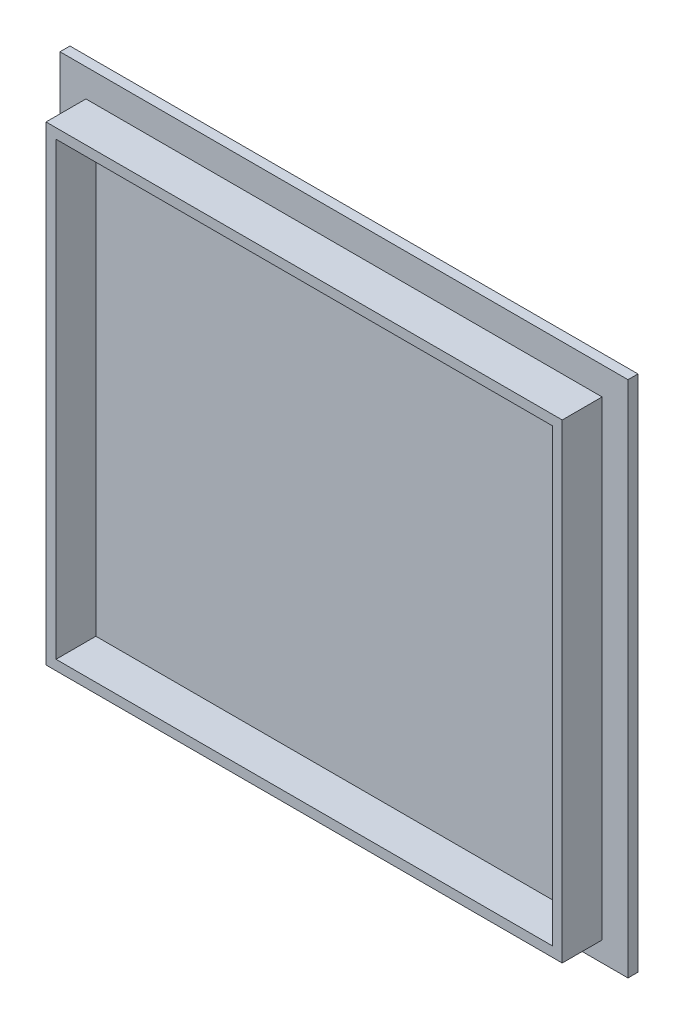
SolidWorks part; units mm, degrees
ref_plane "Front Plane" through (0, 0, 0) normal (0, 0, 1) x (1, 0, 0)
ref_plane "Top Plane" through (0, 0, 0) normal (0, 1, 0) x (1, 0, 0)
ref_plane "Right Plane" through (0, 0, 0) normal (1, 0, 0) x (0, 0, -1)
sketch "Sketch1" plane through (0, 0, 0) normal (0, 0, 1) x (1, 0, 0)
  line L1 (-121.8145, 173.0477) -> (163.1855, 173.0477)
  line L2 (-121.8145, 173.0477) -> (-121.8145, -86.9523)
  line L3 (-121.8145, -86.9523) -> (163.1855, -86.9523)
  line L4 (163.1855, 173.0477) -> (163.1855, -86.9523)
  dimension "D1" = 285
  dimension "D2" = 260
extrude "Boss-Extrude3" add sketch "Sketch1" along normal blind 5
sketch "Sketch3" plane through (0, 0, 5) normal (0, 0, 1) x (1, 0, 0)
  line L0 (163.1855, 173.0477) -> (-121.8145, 173.0477) construction
  line L1 (-108.8145, 159.0477) -> (150.1855, 159.0477)
  line L2 (-108.8145, 159.0477) -> (-108.8145, -76.9523)
  line L3 (-108.8145, -76.9523) -> (150.1855, -76.9523)
  line L4 (150.1855, 159.0477) -> (150.1855, -76.9523)
  line L5 (-121.8145, -86.9523) -> (163.1855, -86.9523) construction
  line L6 (-121.8145, 173.0477) -> (-121.8145, -86.9523) construction
  line L7 (163.1855, -86.9523) -> (163.1855, 173.0477) construction
  dimension "D1" = 14
  dimension "D2" = 10
  dimension "D3" = 13
  dimension "D4" = 13
extrude "Boss-Extrude4" add sketch "Sketch3" along normal blind 20
sketch "Sketch4" plane through (0, 0, 25) normal (0, 0, 1) x (1, 0, 0)
  line L0 (150.1855, 159.0477) -> (-108.8145, 159.0477) construction
  line L1 (-103.8145, 154.0477) -> (145.1855, 154.0477)
  line L2 (-103.8145, 154.0477) -> (-103.8145, -71.9523)
  line L3 (-103.8145, -71.9523) -> (145.1855, -71.9523)
  line L4 (145.1855, 154.0477) -> (145.1855, -71.9523)
  line L5 (150.1855, -76.9523) -> (150.1855, 159.0477) construction
  line L6 (-108.8145, -76.9523) -> (150.1855, -76.9523) construction
  line L7 (-108.8145, 159.0477) -> (-108.8145, -76.9523) construction
  dimension "D1" = 5
  dimension "D2" = 5
  dimension "D3" = 5
  dimension "D4" = 5
extrude "Cut-Extrude1" cut sketch "Sketch4" against normal blind 20
